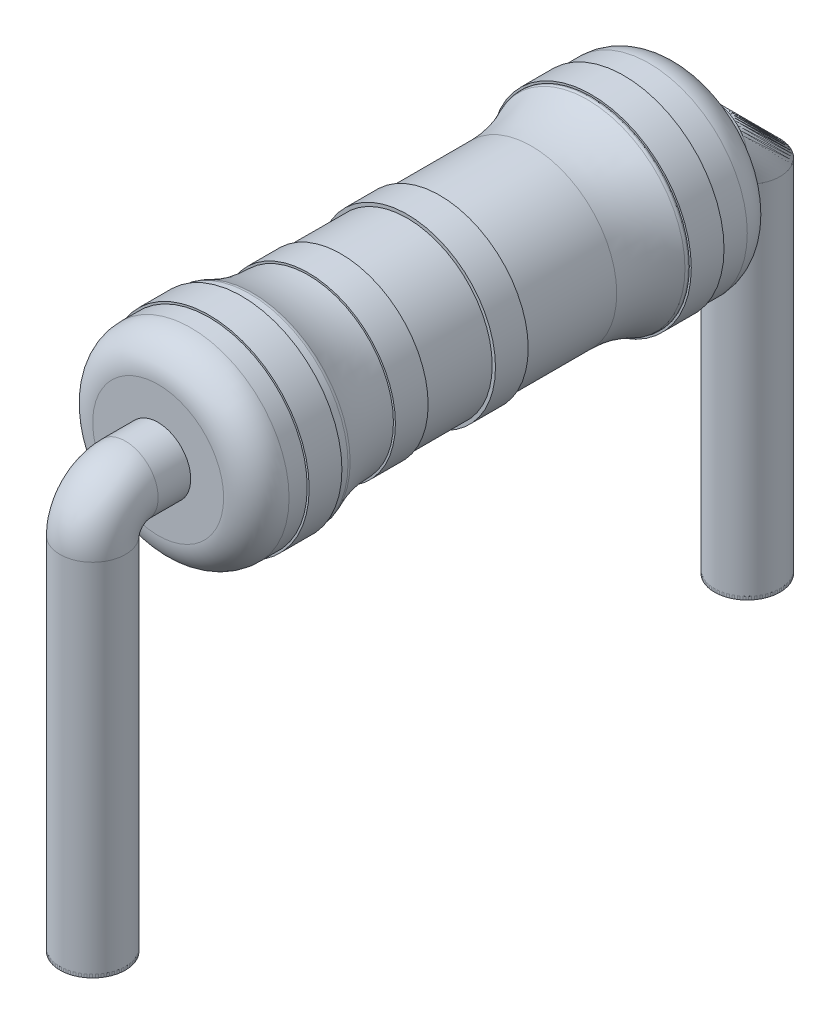
SolidWorks part; units mm, degrees
ref_plane "Front Plane" through (0, 0, 0) normal (0, 0, 1) x (1, 0, 0)
ref_plane "Top Plane" through (0, 0, 0) normal (0, 1, 0) x (1, 0, 0)
ref_plane "Right Plane" through (0, 0, 0) normal (1, 0, 0) x (0, 0, -1)
sketch "Sketch1" plane through (0, 0, 0) normal (1, 0, 0) x (0, 0, -1)
  line L0 (-30.9469, 0) -> (36.7722, 0) construction
  line L1 (2.6, 1.5) -> (3.5, 1.5)
  line L2 (-3.5, 1.5) -> (-2.6, 1.5)
  line L3 (-4, 1) -> (-4, 0)
  line L4 (-4, 0) -> (4, 0)
  line L5 (4, 1) -> (4, 0)
  line L7 (-2.5, 1.4) -> (-2.5, 1.3)
  line L8 (-2.5, 1.3) -> (2.5, 1.3)
  line L9 (2.5, 1.4) -> (2.5, 1.3)
  arc A0 (-3.5, 1.5) -> (-4, 1) centre (-3.5, 1) ccw
  arc A1 (-2.6, 1.5) -> (-2.5, 1.4) centre (-2.6, 1.4) cw
  arc A2 (2.6, 1.5) -> (2.5, 1.4) centre (2.6, 1.4) ccw
  arc A3 (3.5, 1.5) -> (4, 1) centre (3.5, 1) cw
  point P7 (0, 0)
  point P14 (0, 1.3)
  dimension "D3" = 0.5
  dimension "D6" = 0.1
  dimension "D7" = 0.5
  dimension "D1" = 8
  dimension "D2" = 1.5
  dimension "D4" = 5
  dimension "D5" = 0.2
revolve "Revolve1" add sketch "Sketch1" angle 360 about L0
fillet "Fillet1" radius 2 2 edges at (1.3, 0, -2.5) (1.3, 0, 2.5)
sketch "Sketch2" plane through (0, 0, 0) normal (1, 0, 0) x (0, 0, -1)
  line L0 (-2.1847, 0) -> (2.4452, 0) construction
  line L1 (-1.7056, -1.3) -> (-1.7056, 1.3) construction
  line L2 (-1.7056, 1.3) -> (-1.2056, 1.3)
  line L3 (-1.7056, 1.3) -> (-1.7056, 1.33)
  line L4 (-1.7056, 1.33) -> (-1.2056, 1.33)
  line L5 (-1.2056, 1.3) -> (-1.2056, 1.33)
  dimension "D1" = 0.5
revolve "Revolve2" add sketch "Sketch2" angle 360 about L0
sketch "Sketch3" plane through (0, 0, 0) normal (1, 0, 0) x (0, 0, -1)
  line L0 (-0.4894, 0) -> (0.7498, 0) construction
  line L2 (-0.1968, 1.35) -> (0.3032, 1.35)
  line L3 (-0.1968, 1.35) -> (-0.1968, 1.3)
  line L4 (-0.1968, 1.3) -> (0.3032, 1.3)
  line L5 (0.3032, 1.35) -> (0.3032, 1.3)
  dimension "D1" = 0.5
  dimension "D2" = 0.05
  dimension "D3" = 1.3
revolve "Revolve3" add sketch "Sketch3" angle 360 about L0
sketch "Sketch4" plane through (0, 0, 0) normal (1, 0, 0) x (0, 0, -1)
  line L0 (-0.4492, 0) -> (0.4962, 0) construction
  line L1 (-3.2228, 1.53) -> (-2.7228, 1.53)
  line L2 (-3.2228, 1.53) -> (-3.2228, 1.5)
  line L3 (-3.2228, 1.5) -> (-2.7228, 1.5)
  line L4 (-2.7228, 1.53) -> (-2.7228, 1.5)
  dimension "D1" = 0.5
  dimension "D2" = 0.03
  dimension "D3" = 1.5
revolve "Revolve4" add sketch "Sketch4" angle 360 about L0
sketch "Sketch5" plane through (0, 0, 0) normal (1, 0, 0) x (0, 0, -1)
  line L0 (-0.3134, 0) -> (0.3032, 0) construction
  line L1 (2.6145, 1.53) -> (3.1145, 1.53)
  line L2 (2.6145, 1.53) -> (2.6145, 1.5)
  line L3 (2.6145, 1.5) -> (3.1145, 1.5)
  line L4 (3.1145, 1.53) -> (3.1145, 1.5)
  line L5 (0.3032, -1.35) -> (0.3032, 1.35) construction
  dimension "D1" = 0.5
  dimension "D2" = 0.03
  dimension "D3" = 1.5
revolve "Revolve5" add sketch "Sketch5" angle 360 about L0
ref_plane "Plane1" through (0, 0, 4.0029) normal (0, 0, 1) x (1, 0, 0)
sketch "Sketch6" plane through (0, 0, 4.0029) normal (0, 0, 1) x (1, 0, 0)
  circle A0 centre (0, 0) radius 0.5
ref_plane "Plane2" through (0, -6, 0) normal (0, 1, 0) x (-1, 0, 0)
sketch "Sketch7" plane through (0, -6, 0) normal (0, 1, 0) x (-1, 0, 0)
  circle A0 centre (0, 5) radius 0.5
  circle A1 centre (0, 5) radius 0.5
  dimension "D1" = 5
sketch "Sketch8" plane through (0, 0, 0) normal (1, 0, 0) x (0, 0, -1)
  line L0 (-4.0029, 0) -> (-4.5, 0)
  line L1 (-4.0029, 0.5) -> (-4.0029, -0.5) construction
  line L2 (-5, -0.5) -> (-5, -6)
  line L3 (-4.5, -6) -> (-5.5, -6) construction
  arc A0 (-4.5, 0) -> (-5, -0.5) centre (-4.5, -0.5) ccw
  dimension "D1" = 0.5
surface "Surface-Sweep1"
sketch "Sketch9" plane through (0, 0, -4) normal (0, 0, -1) x (-1, 0, 0)
  circle A0 centre (0, 0) radius 0.5
ref_plane "Plane4" through (0, -6, 0) normal (0, 1, 0) x (-1, 0, 0)
sketch "Sketch12" plane through (0, -6, 0) normal (0, 1, 0) x (-1, 0, 0)
  circle A0 centre (0, -5) radius 0.5
  circle A1 centre (0, -5) radius 0.5
  dimension "D1" = 5
sketch "Sketch13" plane through (0, 0, 0) normal (1, 0, 0) x (0, 0, -1)
  line L0 (4, 0) -> (4.5, 0)
  line L1 (4, -0.5) -> (4, 0.5) construction
  line L2 (5, -0.5) -> (5, -6)
  line L3 (5.5, -6) -> (4.5, -6) construction
  arc A0 (4.5, 0) -> (5, -0.5) centre (4.5, -0.5) cw
  dimension "D1" = 0.5
surface "Surface-Sweep3"
extrude "Boss-Extrude1" add sketch "Sketch7" along normal blind 0.05 separate body contours A0
extrude "Boss-Extrude2" add sketch "Sketch12" along normal blind 0.05 separate body contours A0
